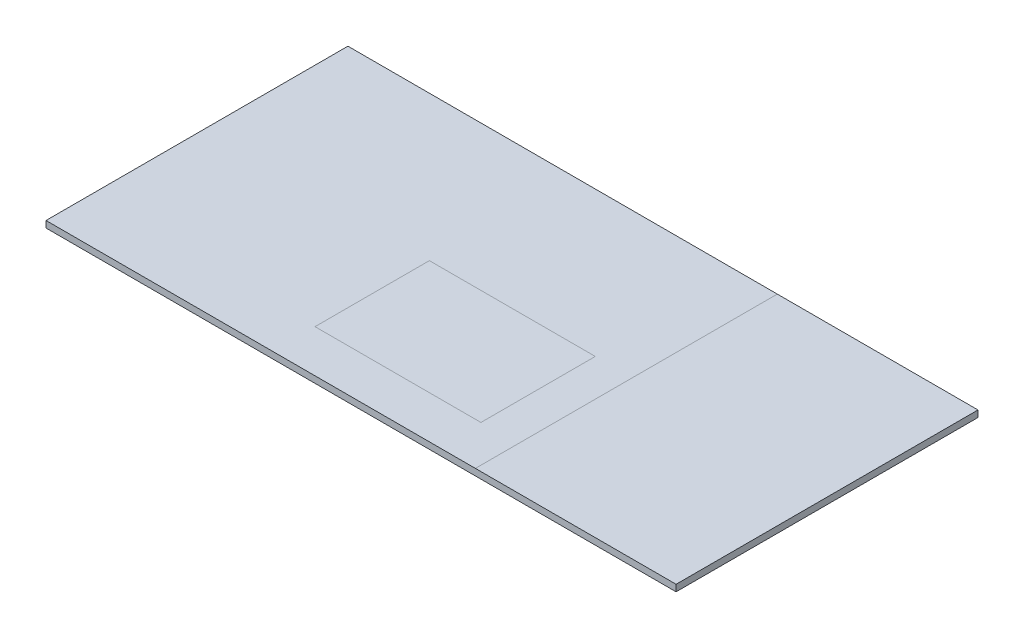
SolidWorks part; units mm, degrees
material "Dövme Paslanmaz Çelik"
ref_plane "Ön Düzlem" through (0, 0, 0) normal (0, 0, 1) x (1, 0, 0)
ref_plane "Üst Düzlem" through (0, 0, 0) normal (0, 1, 0) x (1, 0, 0)
ref_plane "Sağ Düzlem" through (0, 0, 0) normal (1, 0, 0) x (0, 0, -1)
sketch "Çizim2" plane through (0, 0, 0) normal (0, 1, 0) x (1, 0, 0)
  line L5 (0, 0) -> (1920, 0)
  line L6 (0, 0) -> (0, 920)
  line L7 (0, 920) -> (1920, 920)
  line L8 (1920, 0) -> (1920, 920)
  dimension "D1" = 920
  dimension "D2" = 1920
extrude "Yükseklik-Ekstrüzyon2" add sketch "Çizim2" along normal blind 20
sketch "Çizim3" plane through (0, 20, 0) normal (0, 1, 0) x (1, 0, 0)
  line L1 (690.0992, 478.1277) -> (1195.6597, 478.1277)
  line L2 (690.0992, 478.1277) -> (690.0992, 129.6736)
  line L3 (690.0992, 129.6736) -> (1195.6597, 129.6736)
  line L4 (1195.6597, 478.1277) -> (1195.6597, 129.6736)
split line "Ayrım Çizgisi1"
sketch "Çizim4" plane through (0, 20, 0) normal (0, 1, 0) x (1, 0, 0)
  line L0 (1308.4541, 920) -> (1308.4541, 0)
  line L1 (1920, 920) -> (0, 920) construction
  line L2 (0, 0) -> (1920, 0) construction
split line "Ayrım Çizgisi2"
